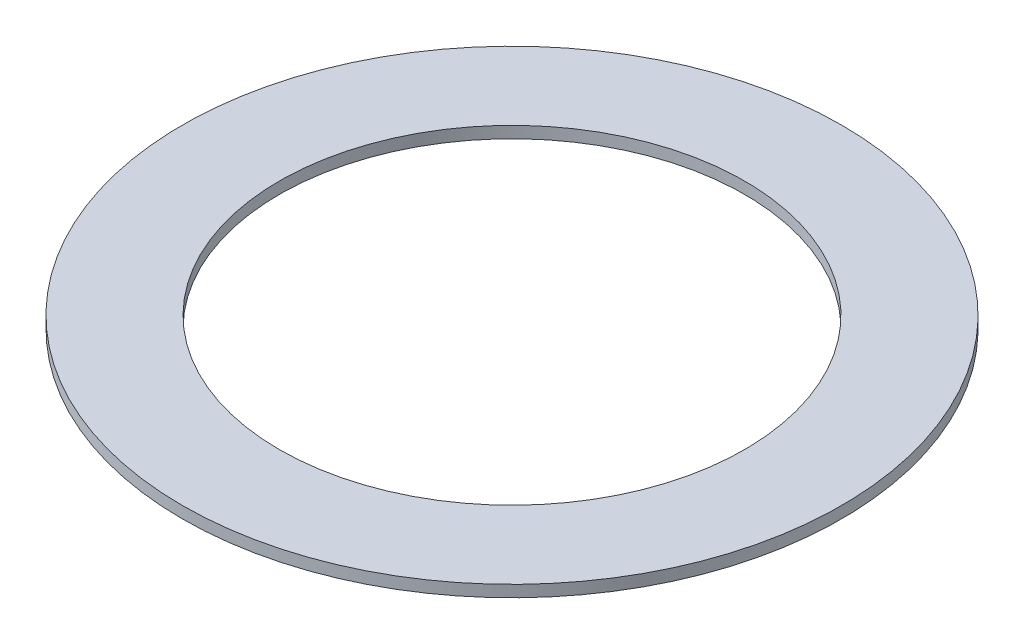
SolidWorks part; units mm, degrees
material "Plain Carbon Steel"
ref_plane "Front Plane" through (0, 0, 0) normal (0, 0, 1) x (1, 0, 0)
ref_plane "Top Plane" through (0, 0, 0) normal (0, 1, 0) x (1, 0, 0)
ref_plane "Right Plane" through (0, 0, 0) normal (1, 0, 0) x (0, 0, -1)
sketch "Sketch1" plane through (0, 0, 0) normal (0, 1, 0) x (1, 0, 0)
  circle A0 centre (0, 0) radius 38.1
  circle A1 centre (0, 0) radius 53.975
  dimension "D1" = 76.2
  dimension "D2" = 107.95
extrude "Boss-Extrude1" add sketch "Sketch1" along normal blind 1.905
